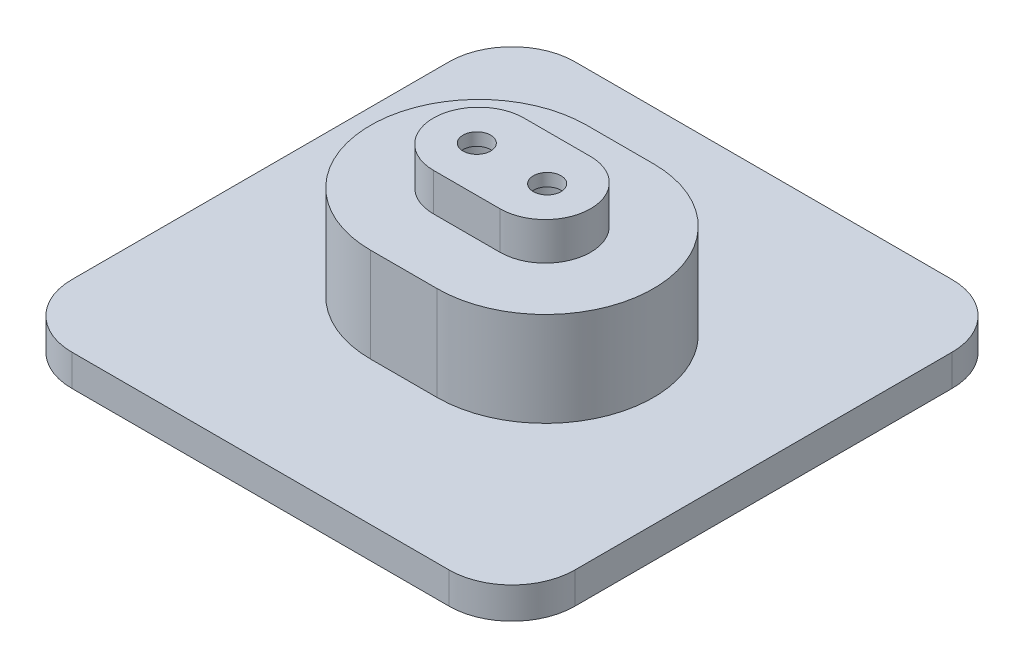
SolidWorks part; units mm, degrees
ref_plane "Front Plane" through (0, 0, 0) normal (0, 0, 1) x (1, 0, 0)
ref_plane "Top Plane" through (0, 0, 0) normal (0, 1, 0) x (1, 0, 0)
ref_plane "Right Plane" through (0, 0, 0) normal (1, 0, 0) x (0, 0, -1)
sketch "Sketch1" plane through (0, 0, 0) normal (0, 1, 0) x (1, 0, 0)
  line L1 (30, -40) -> (-30, -40)
  line L2 (40, -30) -> (40, 30)
  line L3 (30, 40) -> (-30, 40)
  line L4 (-40, -30) -> (-40, 30)
  line L5 (40, -40) -> (-40, 40) construction
  line L6 (40, 40) -> (-40, -40) construction
  arc A0 (-30, -40) -> (-40, -30) centre (-30, -30) cw
  arc A1 (30, -40) -> (40, -30) centre (30, -30) ccw
  arc A2 (40, 30) -> (30, 40) centre (30, 30) ccw
  arc A3 (-30, 40) -> (-40, 30) centre (-30, 30) ccw
  point P0 (0, 0)
  dimension "D3" = 10
  dimension "D1" = 80
  dimension "D2" = 80
extrude "Boss-Extrude1" add sketch "Sketch1" along normal blind 5
sketch "Sketch3" plane through (0, 5, 0) normal (0, 1, 0) x (1, 0, 0)
  line L0 (-5.2995, 0) -> (5.2995, 0) construction
  line L1 (-5.2995, 7.2005) -> (5.2995, 7.2005) construction
  line L2 (-5.2995, -7.2005) -> (5.2995, -7.2005) construction
  line L3 (-12.5, 0) -> (-12.5, 11.315) construction
  line L4 (12.5, 0) -> (12.5, 11.315) construction
  arc A0 (-5.2995, 7.2005) -> (-5.2995, -7.2005) centre (-5.2995, 0) ccw construction
  arc A1 (5.2995, -7.2005) -> (5.2995, 7.2005) centre (5.2995, 0) ccw construction
  point P3 (0, 0)
  point P12 (0, 0)
  point P13 (0, 0)
  dimension "D2" = 25
  dimension "D1" = 14.4009
sketch "Sketch4" plane through (0, 5, 0) normal (0, 1, 0) x (1, 0, 0)
  line L6 (-5.2995, -17.2005) -> (5.2995, -17.2005)
  line L7 (5.2995, 17.2005) -> (-5.2995, 17.2005)
  line L8 (-5.2995, -17.2005) -> (5.2995, -17.2005)
  line L9 (5.2995, 17.2005) -> (-5.2995, 17.2005)
  arc A8 (-5.2995, 17.2005) -> (-5.2995, -17.2005) centre (-5.2995, 0) ccw
  arc A9 (5.2995, -17.2005) -> (5.2995, 17.2005) centre (5.2995, 0) ccw
  arc A10 (-5.2995, 17.2005) -> (-5.2995, -17.2005) centre (-5.2995, 0) ccw
  arc A11 (5.2995, -17.2005) -> (5.2995, 17.2005) centre (5.2995, 0) ccw
  dimension "D1" = 10
extrude "Boss-Extrude2" add sketch "Sketch4" along normal blind 15
ref_plane "Plane1" through (0, 26, 0) normal (0, -1, 0) x (-1, 0, 0)
sketch "Sketch5" plane through (0, 20, 0) normal (0, 1, 0) x (1, 0, 0)
  line L4 (-5.2995, -7.2005) -> (5.2995, -7.2005)
  line L5 (5.2995, 7.2005) -> (-5.2995, 7.2005)
  line L6 (-5.2995, -7.2005) -> (5.2995, -7.2005)
  line L7 (5.2995, 7.2005) -> (-5.2995, 7.2005)
  arc A4 (-5.2995, 7.2005) -> (-5.2995, -7.2005) centre (-5.2995, 0) ccw
  arc A5 (5.2995, -7.2005) -> (5.2995, 7.2005) centre (5.2995, 0) ccw
  arc A6 (-5.2995, 7.2005) -> (-5.2995, -7.2005) centre (-5.2995, 0) ccw
  arc A7 (5.2995, -7.2005) -> (5.2995, 7.2005) centre (5.2995, 0) ccw
  dimension "D1" = 10
extrude "Boss-Extrude3" add sketch "Sketch5" along normal up to surface (6 mm away) up to plane "Plane1"
sketch "Sketch6" plane through (0, 26, 0) normal (0, 1, 0) x (1, 0, 0)
  line L0 (-5.2995, 0) -> (5.2995, 0) construction
  line L1 (0, -0.3513) -> (0, -9.576) construction
  circle A0 centre (-5.595, 0) radius 2.2
  circle A1 centre (5.595, 0) radius 2.2
  point P6 (0, 0)
  dimension "D1" = 4.4
  dimension "D2" = 11.19
extrude "Cut-Extrude1" cut sketch "Sketch6" against normal blind 27 contours A1 | A0
sketch "Sketch7" plane through (0, 0, 0) normal (0, -1, 0) x (1, 0, 0)
  circle A0 centre (5.595, 0) radius 4.1
  circle A1 centre (-5.595, 0) radius 4.1
  dimension "D1" = 8.2
extrude "Cut-Extrude2" cut sketch "Sketch7" against normal offset from surface (24 mm away) 2 up to face at (5.595, 26, 2.2)
